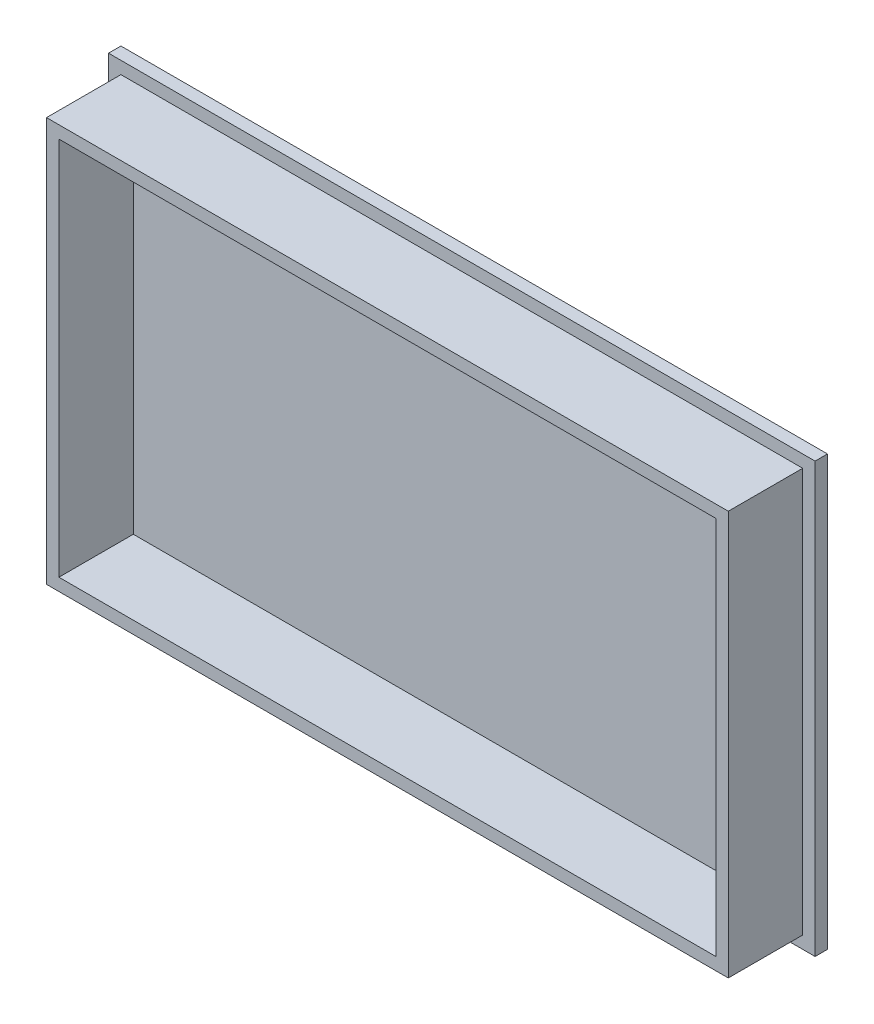
SolidWorks part; units mm, degrees
ref_plane "Front Plane" through (0, 0, 0) normal (0, 0, 1) x (1, 0, 0)
ref_plane "Top Plane" through (0, 0, 0) normal (0, 1, 0) x (1, 0, 0)
ref_plane "Right Plane" through (0, 0, 0) normal (1, 0, 0) x (0, 0, -1)
sketch "Sketch2" plane through (0, 0, 0) normal (0, 0, 1) x (1, 0, 0)
  line L1 (-136.6271, 69.8391) -> (148.2729, 69.8391)
  line L2 (-136.6271, 69.8391) -> (-136.6271, -103.1609)
  line L3 (-136.6271, -103.1609) -> (148.2729, -103.1609)
  line L4 (148.2729, 69.8391) -> (148.2729, -103.1609)
  dimension "D1" = 284.9
  dimension "D2" = 173
extrude "Boss-Extrude1" add sketch "Sketch2" along normal blind 5
sketch "Sketch3" plane through (0, 0, 5) normal (0, 0, 1) x (1, 0, 0)
  line L0 (148.2729, 69.8391) -> (-136.6271, 69.8391) construction
  line L1 (-131.6271, 64.8391) -> (143.2729, 64.8391)
  line L2 (-131.6271, 64.8391) -> (-131.6271, -98.1609)
  line L3 (-131.6271, -98.1609) -> (143.2729, -98.1609)
  line L4 (143.2729, 64.8391) -> (143.2729, -98.1609)
  line L5 (-136.6271, 69.8391) -> (-136.6271, -103.1609) construction
  line L6 (-136.6271, -103.1609) -> (148.2729, -103.1609) construction
  line L7 (148.2729, -103.1609) -> (148.2729, 69.8391) construction
  dimension "D1" = 5
  dimension "D2" = 5
  dimension "D3" = 5
  dimension "D4" = 5
  dimension "D5" = 163
extrude "Boss-Extrude2" add sketch "Sketch3" along normal blind 30
sketch "Sketch4" plane through (0, 0, 35) normal (0, 0, 1) x (1, 0, 0)
  line L0 (143.2729, 64.8391) -> (-131.6271, 64.8391) construction
  line L1 (-126.6271, 59.8391) -> (138.2729, 59.8391)
  line L2 (-126.6271, 59.8391) -> (-126.6271, -93.1609)
  line L3 (-126.6271, -93.1609) -> (138.2729, -93.1609)
  line L4 (138.2729, 59.8391) -> (138.2729, -93.1609)
  line L5 (-131.6271, -98.1609) -> (143.2729, -98.1609) construction
  line L6 (143.2729, -98.1609) -> (143.2729, 64.8391) construction
  line L7 (-131.6271, 64.8391) -> (-131.6271, -98.1609) construction
  dimension "D1" = 5
  dimension "D2" = 5
  dimension "D3" = 5
  dimension "D4" = 5
extrude "Cut-Extrude1" cut sketch "Sketch4" against normal blind 30
